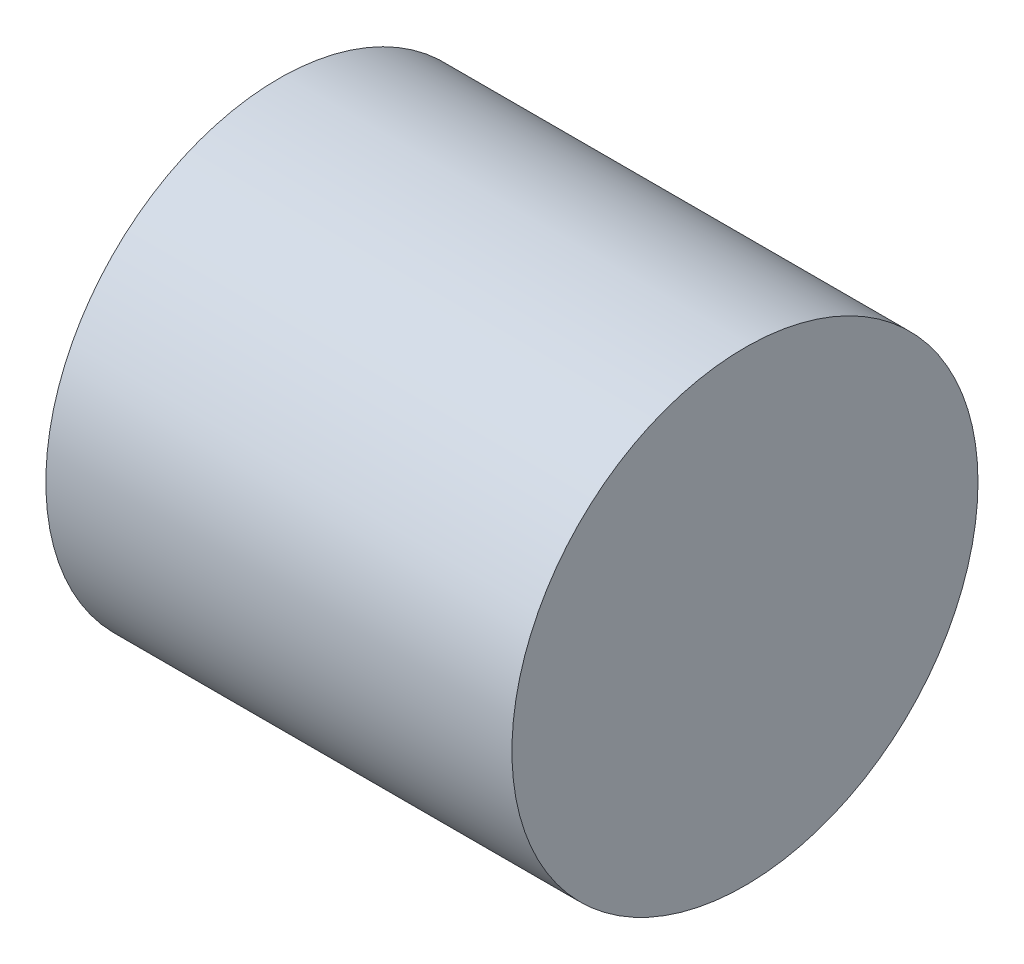
SolidWorks part; units mm, degrees
ref_plane "Plan de face" through (0, 0, 0) normal (0, 0, 1) x (1, 0, 0)
ref_plane "Plan de dessus" through (0, 0, 0) normal (0, 1, 0) x (1, 0, 0)
ref_plane "Plan de droite" through (0, 0, 0) normal (1, 0, 0) x (0, 0, -1)
sketch "Esquisse1" plane through (0, 0, 0) normal (1, 0, 0) x (0, 0, -1)
  circle A0 centre (0, 0) radius 5
extrude "Boss.-Extru.1" add sketch "Esquisse1" along normal blind 10
